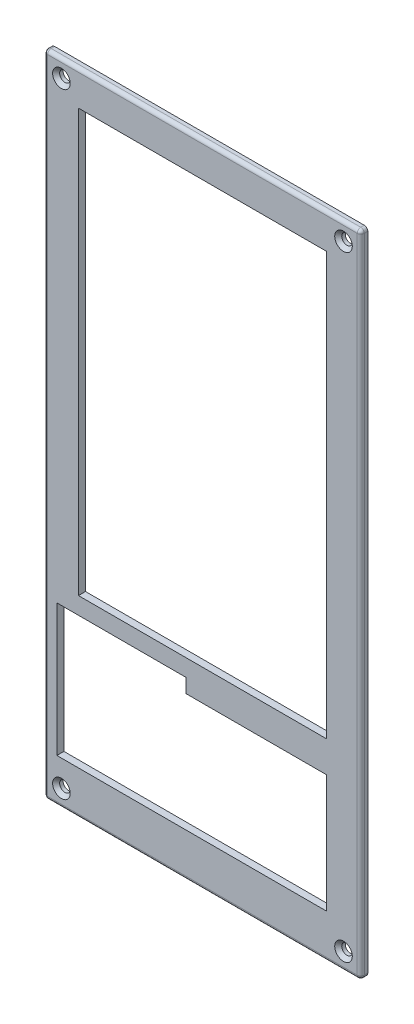
SolidWorks part; units mm, degrees
material "ABS"
ref_plane "Ön Düzlem" through (0, 0, 0) normal (1, 0, 0) x (0, 1, 0)
ref_plane "Üst Düzlem" through (0, 0, 0) normal (0, 0, 1) x (0, 1, 0)
ref_plane "Sağ Düzlem" through (0, 0, 0) normal (0, 1, 0) x (-1, 0, 0)
sketch "Çizim1" plane through (0, 0, 0) normal (0, 0, 1) x (0, 1, 0)
  line L0 (-1, 0) -> (-183.6, 0)
  line L1 (-184.6, -1) -> (-184.6, -89)
  line L2 (-183.6, -90) -> (-1, -90)
  line L3 (0, -89) -> (0, -1)
  arc A0 (-1, -90) -> (0, -89) centre (-1, -89) ccw
  arc A1 (-184.6, -89) -> (-183.6, -90) centre (-183.6, -89) ccw
  arc A2 (-1, 0) -> (0, -1) centre (-1, -1) cw
  arc A3 (-183.6, 0) -> (-184.6, -1) centre (-183.6, -1) ccw
  circle A12 centre (-179.6936, -4.9064) radius 1.5
  circle A13 centre (-179.6936, -4.9064) radius 1.5
  circle A15 centre (-4.9064, -4.9064) radius 1.5
  circle A17 centre (-179.6936, -85.0936) radius 1.5
  circle A19 centre (-4.9064, -85.0936) radius 1.5
  point P11 (0, 0)
extrude "Ön Panel" add sketch "Çizim1" along normal blind 2
chamfer "Vida Delikleri 45derece Pah 1mm" distance 1 angle 45 4 edges at (86.5936, -4.9064, 2) (6.4064, -4.9064, 2) (6.4064, -179.6936, 2) (86.5936, -179.6936, 2)
sketch "Çizim2" plane through (0, 0, 2) normal (0, 0, 1) x (1, 0, 0)
  line L2 (9.7577, -9.7984) -> (80.2423, -9.7984)
  line L3 (9.7577, -9.7984) -> (9.7577, -129.7984)
  line L4 (80.2423, -9.7984) -> (80.2423, -129.7984)
  line L5 (80.2423, -129.7984) -> (9.7577, -129.7984)
  line L6 (40.317, -138.6537) -> (40.317, -134.6537)
  line L11 (40.317, -134.6537) -> (3.6162, -134.6537)
  line L12 (3.6162, -134.6537) -> (3.6162, -172.2244)
  line L15 (80.2423, -138.6537) -> (40.317, -138.6537)
  line L17 (3.6162, -172.2244) -> (80.2423, -172.2244)
  line L18 (80.2423, -172.2244) -> (80.2423, -138.6537)
  dimension "D1" = 120
  dimension "D2" = 70.4845
  dimension "D3" = 76.626
  dimension "D4" = 37.5707
  dimension "D5" = 33.5707
extrude "Ekran ve Kontrolcü delikleri" cut sketch "Çizim2" against normal blind 2
fillet "Fillet1" radius 1 8 edges at (0, -92.3, 2) (0.2929, -184.3071, 2) (45, -184.6, 2) (89.7071, -184.3071, 2) (90, -92.3, 2) (89.7071, -0.2929, 2) (45, 0, 2) (0.2929, -0.2929, 2)
